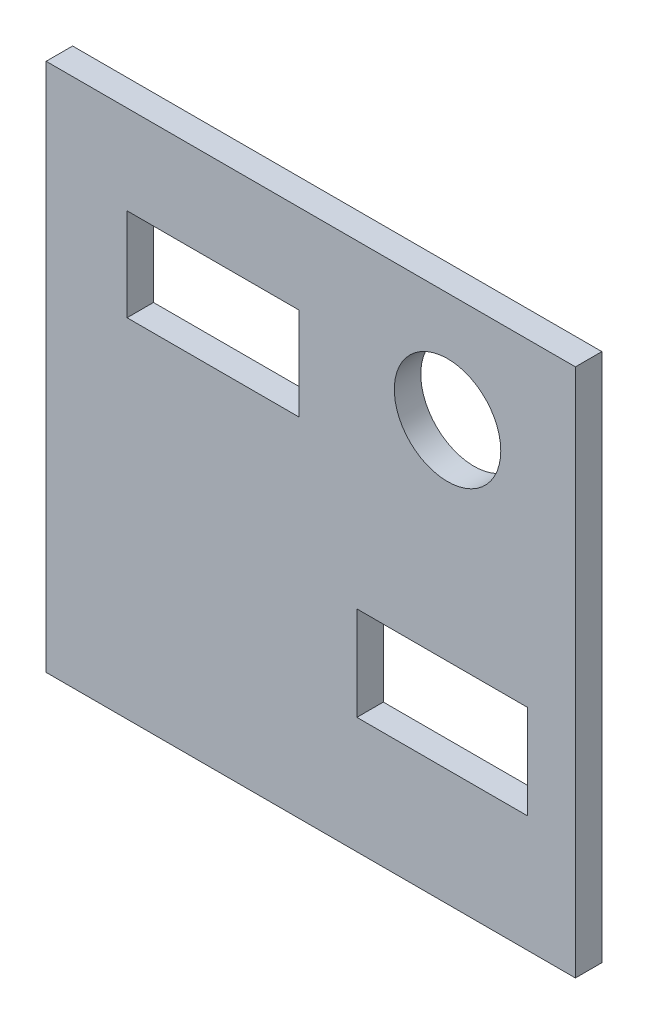
SolidWorks part; units mm, degrees
ref_plane "Front Plane" through (0, 0, 0) normal (0, 0, 1) x (1, 0, 0)
ref_plane "Top Plane" through (0, 0, 0) normal (0, 1, 0) x (1, 0, 0)
ref_plane "Right Plane" through (0, 0, 0) normal (1, 0, 0) x (0, 0, -1)
sketch "Sketch1" plane through (0, 0, 0) normal (0, 0, 1) x (1, 0, 0)
  line L1 (-17.9817, 13.6391) -> (22.0183, 13.6391)
  line L2 (-17.9817, 13.6391) -> (-17.9817, -26.3609)
  line L3 (-17.9817, -26.3609) -> (22.0183, -26.3609)
  line L4 (22.0183, 13.6391) -> (22.0183, -26.3609)
  line L5 (-11.8654, 6.9113) -> (1.1346, 6.9113)
  line L6 (-11.8654, 6.9113) -> (-11.8654, -0.0887)
  line L7 (-11.8654, -0.0887) -> (1.1346, -0.0887)
  line L8 (1.1346, 6.9113) -> (1.1346, -0.0887)
  line L9 (5.5046, -10.4587) -> (18.4046, -10.4587)
  line L10 (5.5046, -10.4587) -> (5.5046, -17.5587)
  line L11 (5.5046, -17.5587) -> (18.4046, -17.5587)
  line L12 (18.4046, -10.4587) -> (18.4046, -17.5587)
  circle A0 centre (12.3547, 5.3211) radius 4.0237
  point P14 (-11.8654, 6.9113)
  dimension "D1" = 40
  dimension "D2" = 40
  dimension "D3" = 13
  dimension "D4" = 7
  dimension "D5" = 12.9
  dimension "D6" = 7.1
extrude "Boss-Extrude1" add sketch "Sketch1" along normal blind 2
